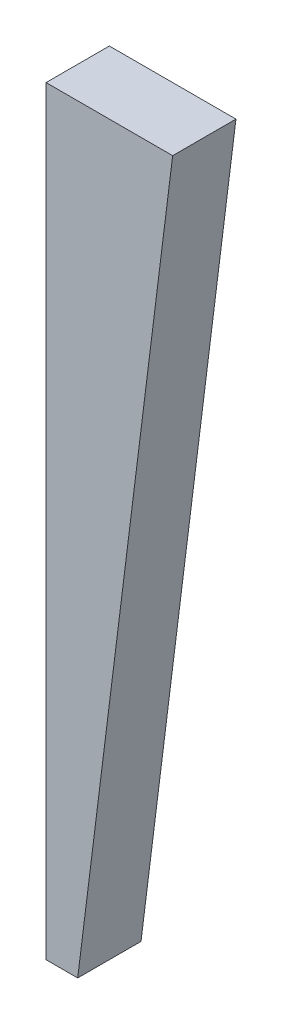
SolidWorks part; units mm, degrees
ref_plane "Front Plane" through (0, 0, 0) normal (0, 0, 1) x (1, 0, 0)
ref_plane "Top Plane" through (0, 0, 0) normal (0, 1, 0) x (1, 0, 0)
ref_plane "Right Plane" through (0, 0, 0) normal (1, 0, 0) x (0, 0, -1)
sketch "Sketch1" plane through (0, 0, 0) normal (0, 0, 1) x (1, 0, 0)
  line L0 (0, 0) -> (12.7, 0)
  line L1 (12.7, 0) -> (3.175, -76.2)
  line L2 (3.175, -76.2) -> (0, -76.2)
  line L3 (0, -76.2) -> (0, 0)
  dimension "D1" = 12.7
  dimension "D2" = 3.175
  dimension "D3" = 76.2
extrude "Boss-Extrude1" add sketch "Sketch1" along normal blind 6.35
